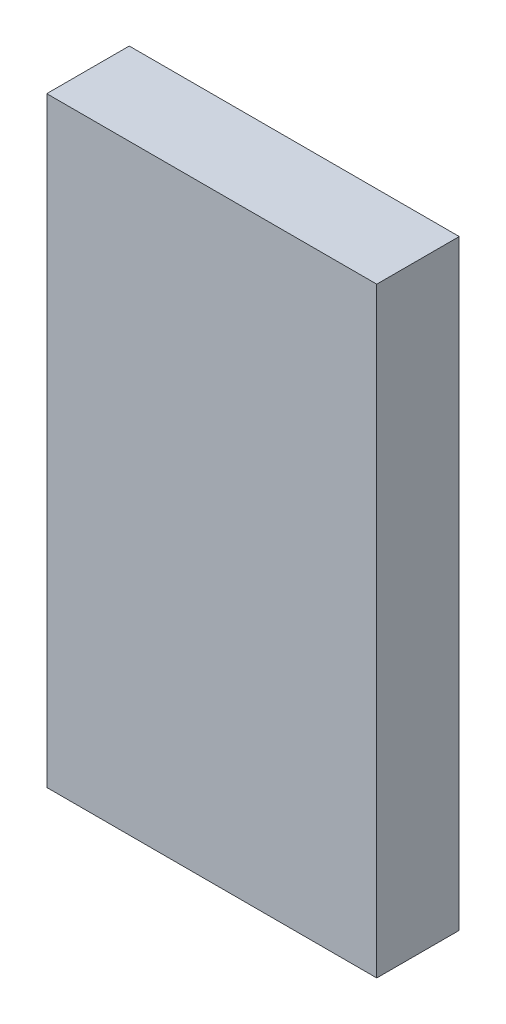
SolidWorks part; units mm, degrees
ref_plane "Přední rovina" through (0, 0, 0) normal (0, 0, 1) x (1, 0, 0)
ref_plane "Horní rovina" through (0, 0, 0) normal (0, 1, 0) x (1, 0, 0)
ref_plane "Pravá rovina" through (0, 0, 0) normal (1, 0, 0) x (0, 0, -1)
sketch "Skica1" plane through (0, 0, 0) normal (0, 1, 0) x (1, 0, 0)
  line L1 (-5.08, -1.27) -> (5.08, -1.27)
  line L2 (-5.08, -1.27) -> (-5.08, 1.27)
  line L3 (-5.08, 1.27) -> (5.08, 1.27)
  line L4 (5.08, -1.27) -> (5.08, 1.27)
  line L5 (-5.08, -1.27) -> (5.08, 1.27) construction
  line L6 (-5.08, 1.27) -> (5.08, -1.27) construction
  point P0 (0, 0)
  dimension "D1" = 10.16
  dimension "D2" = 2.54
extrude "Přidat vysunutím1" add sketch "Skica1" along normal blind 18.5
